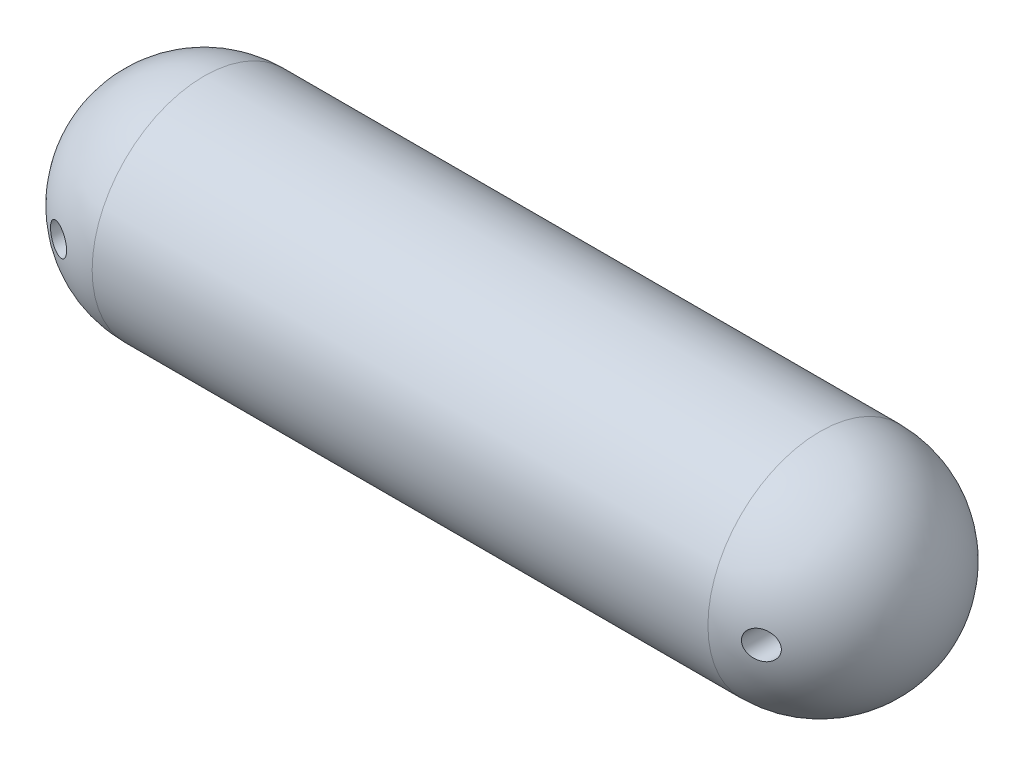
SolidWorks part; units mm, degrees
material "Aleación 2014"
ref_plane "Alzado" through (0, 0, 0) normal (0, 0, 1) x (1, 0, 0)
ref_plane "Planta" through (0, 0, 0) normal (0, 1, 0) x (1, 0, 0)
ref_plane "Vista lateral" through (0, 0, 0) normal (1, 0, 0) x (0, 0, -1)
sketch "Croquis3" plane through (0, 0, 0) normal (0, 1, 0) x (1, 0, 0)
  line L0 (-63.0853, 0) -> (72.028, 0) construction
  line L2 (-2.9193, 0) -> (17.0807, 0) construction
  line L5 (147.0807, 0) -> (47.0807, 0) construction
  line L6 (17.0807, 20) -> (107.0807, 20)
  line L8 (147.0807, 0) -> (127.0807, 0) construction
  line L11 (-2.9193, 0) -> (147.0807, 0)
  line L12 (127.0807, 20) -> (107.0807, 20)
  arc A4 (17.0807, 20) -> (-2.9193, 0) centre (17.0807, 0) ccw
  arc A8 (147.0807, 0) -> (127.0807, 20) centre (127.0807, 0) ccw
  dimension "D2" = 20
  dimension "D4" = 150
revolve "Revolución10" add sketch "Croquis3" angle 360 about L0
sketch "Croquis6" plane through (0, 0, 0) normal (0, 0, 1) x (1, 0, 0)
  line L0 (72.0807, 32.201) -> (72.0807, -35.8143) construction
  line L1 (127.0807, -20) -> (17.0807, -20) construction
  line L2 (4.3048, 0) -> (9.3048, 0) construction
  circle A3 centre (9.3048, 0) radius 2.5
  circle A4 centre (134.8567, 0) radius 2.5
  dimension "D2" = 5
  dimension "D1" = 5
extrude "Cortar-Extruir1" cut sketch "Croquis6" against normal through all both and the other way through all
